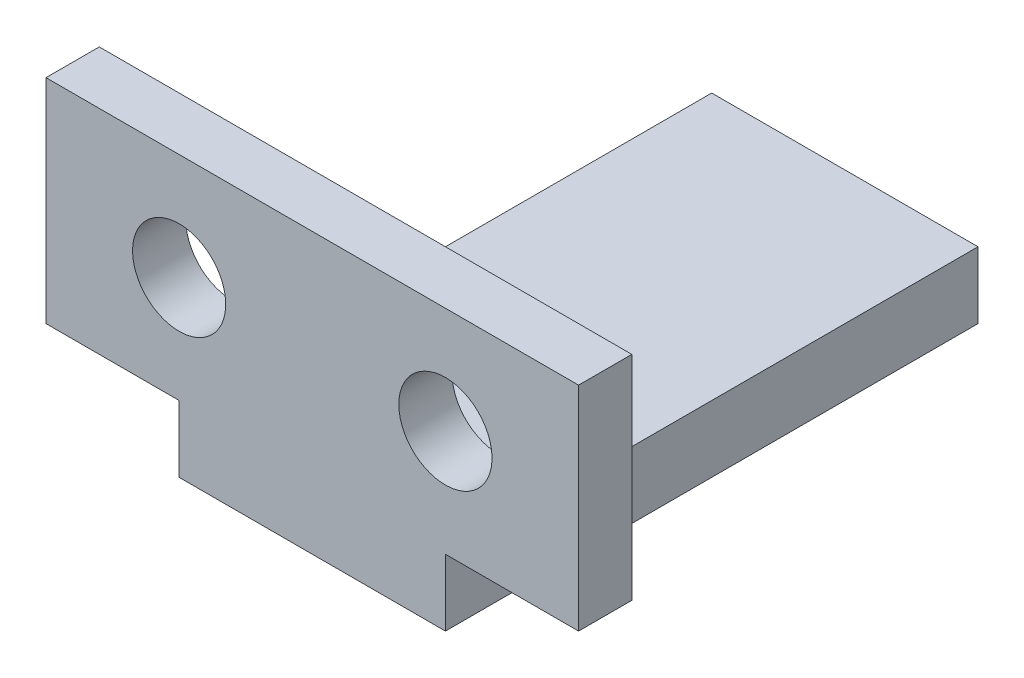
SolidWorks part; units mm, degrees
ref_plane "前视基准面" through (0, 0, 0) normal (0, 0, 1) x (1, 0, 0)
ref_plane "上视基准面" through (0, 0, 0) normal (0, 1, 0) x (1, 0, 0)
ref_plane "右视基准面" through (0, 0, 0) normal (1, 0, 0) x (0, 0, -1)
sketch "草图1" plane through (0, 0, 0) normal (0, 0, 1) x (1, 0, 0)
  line L1 (0, 0) -> (20, 0)
  line L2 (0, 0) -> (0, 8)
  line L3 (0, 8) -> (20, 8)
  line L4 (20, 0) -> (20, 8)
  dimension "D1" = 20
  dimension "D2" = 8
extrude "凸台-拉伸1" add sketch "草图1" along normal blind 2
sketch "草图2" plane through (0, 0, 2) normal (0, 0, 1) x (1, 0, 0)
  line L0 (0, 0) -> (20, 0) construction
  line L1 (5, 0) -> (15, 0)
  line L2 (5, 0) -> (5, -2.5)
  line L3 (5, -2.5) -> (15, -2.5)
  line L4 (15, 0) -> (15, -2.5)
  line L5 (10, 8) -> (10, -12.6225) construction
  line L6 (20, 8) -> (0, 8) construction
  dimension "D1" = 10
  dimension "D2" = 2.5
extrude "凸台-拉伸2" add sketch "草图2" against normal blind 20
sketch "草图3" plane through (0, 0, 0) normal (0, 0, -1) x (-1, 0, 0)
  line L0 (-10, 8) -> (-10, 0) construction
  line L1 (-20, 8) -> (0, 8) construction
  line L2 (-15, 0) -> (-5, 0) construction
  circle A0 centre (-15, 4) radius 1.75
  circle A1 centre (-5, 4) radius 1.75
  dimension "D2" = 3.5
  dimension "D1" = 10
  dimension "D3" = 4
extrude "切除-拉伸1" cut sketch "草图3" against normal blind 20
